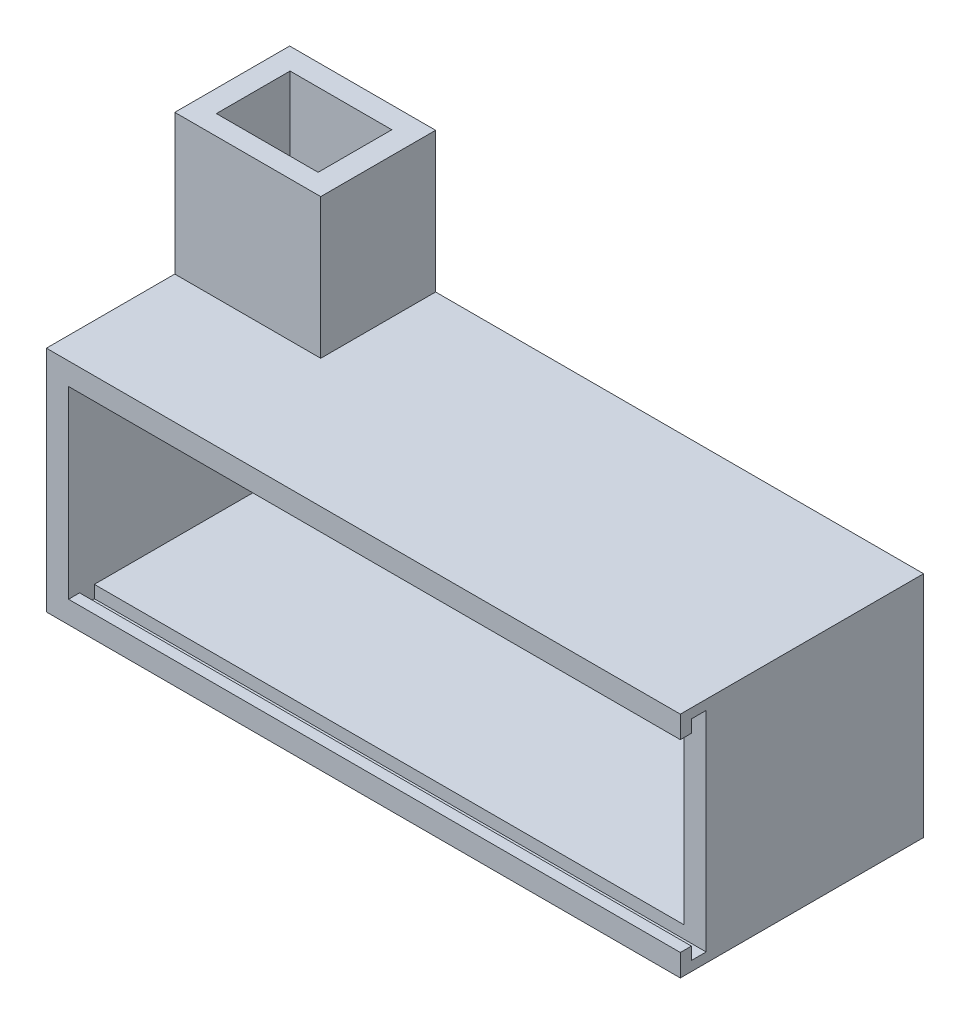
SolidWorks part; units mm, degrees
other "Marquage1"
sketch "Esquisse9" plane through (3, -3, 30) normal (0.8124, -0.2477, 0.5279) x (0.3571, 0.927, -0.1146)
ref_plane "Plan de face" through (0, 0, 0) normal (0, 0, 1) x (1, 0, 0)
ref_plane "Plan de dessus" through (0, 0, 0) normal (0, 1, 0) x (1, 0, 0)
ref_plane "Plan de droite" through (0, 0, 0) normal (1, 0, 0) x (0, 0, -1)
sketch "Esquisse1" plane through (0, 0, 0) normal (0, 0, 1) x (1, 0, 0)
  line L1 (0, 0) -> (-80, 0)
  line L2 (0, 0) -> (0, 25)
  line L3 (0, 25) -> (-80, 25)
  line L4 (-80, 0) -> (-80, 25)
  dimension "D1" = 80
  dimension "D2" = 25
extrude "Boss.-Extru.1" add sketch "Esquisse1" along normal blind 4
ref_plane "Plan1" through (0, 0, 0) normal (0, 0, -1) x (-1, 0, 0)
sketch "Esquisse3" plane through (0, 0, 0) normal (0, 0, -1) x (-1, 0, 0)
  line L0 (80, 25) -> (80, 0) construction
  line L1 (0, 0) -> (80, 0)
  line L2 (0, 0) -> (0, -3)
  line L3 (0, -3) -> (80, -3)
  line L4 (80, 0) -> (80, -3)
  dimension "D1" = 3
extrude "Boss.-Extru.2" add sketch "Esquisse3" against normal blind 28
ref_plane "Plan3" through (0, 12.5, 0) normal (0, 1, 0) x (1, 0, 0)
mirror "Symétrie1" about plane through (0, 12.5, 0) normal (0, 1, 0) of "Boss.-Extru.2"
sketch "Esquisse4" plane through (0, 0, 0) normal (1, 0, 0) x (0, 0, -1)
  line L1 (-28, 28) -> (0, 28)
  line L2 (-28, 28) -> (-28, -3)
  line L3 (-28, -3) -> (0, -3)
  line L4 (0, 28) -> (0, -3)
extrude "Boss.-Extru.3" add sketch "Esquisse4" along normal blind 3
sketch "Esquisse5" plane through (-80, 0, 0) normal (-1, 0, 0) x (0, 0, 1)
  line L1 (0, 28) -> (28, 28)
  line L2 (0, 28) -> (0, -3)
  line L3 (0, -3) -> (28, -3)
  line L4 (28, 28) -> (28, -3)
extrude "Boss.-Extru.4" add sketch "Esquisse5" along normal blind 3
sketch "Esquisse6" plane through (3, 0, 0) normal (1, 0, 0) x (0, 0, -1)
  line L0 (-33, 0) -> (-31.5, 0)
  line L1 (-28, -3) -> (-33, -3)
  line L2 (-28, -3) -> (-28, 0)
  line L3 (-28, 0) -> (-29.5, 0)
  line L4 (-33, -3) -> (-33, 0)
  line L5 (-31.5, 0) -> (-31.5, -1.6912)
  line L6 (-31.5, -1.6912) -> (-29.5, -1.6912)
  line L7 (-29.5, -1.6912) -> (-29.5, 0)
  line L8 (-29.5, 0) -> (-28, 0)
  line L9 (-31.5, 0) -> (-33, 0)
  line M7 (-28, 28) -> (-28, -3)
  dimension "D1" = 5
  dimension "D2" = 1.5
  dimension "D3" = 2
extrude "Boss.-Extru.5" add sketch "Esquisse6" against normal up to surface (86 mm away) contours L7 L6 L5 L0 L4 L1 L3 M7 up to face at (-83, 12.5, 14)
sketch "Esquisse7" plane through (-83, 0, 0) normal (-1, 0, 0) x (0, 0, 1)
  line L1 (28, 0) -> (33, 0)
  line L2 (28, 0) -> (28, -3)
  line L3 (28, -3) -> (33, -3)
  line L4 (33, 0) -> (33, -3)
extrude "Boss.-Extru.6" add sketch "Esquisse7" against normal up to surface (3 mm away) up to face at (-80, 12.5, 16)
mirror "Symétrie2" about plane through (0, 12.5, 0) normal (0, 1, 0) of "Boss.-Extru.6", "Boss.-Extru.5"
sketch "Esquisse8" plane through (0, 25, 0) normal (0, -1, 0) x (1, 0, 0)
  line L1 (-83, 33) -> (-80, 33)
  line L2 (-83, 33) -> (-83, 28)
  line L3 (-83, 28) -> (-80, 28)
  line L4 (-80, 33) -> (-80, 28)
extrude "Boss.-Extru.7" add sketch "Esquisse8" along normal up to surface (25 mm away) up to face at (-39.5, 0, 25.6667)
sketch "Esquisse10" plane through (0, 0, 28) normal (0, 0, 1) x (1, 0, 0)
  line L1 (0, 25) -> (3, 25)
  line L2 (0, 25) -> (0, 0)
  line L3 (0, 0) -> (3, 0)
  line L4 (3, 25) -> (3, 0)
extrude "Boss.-Extru.8" add sketch "Esquisse10" along normal up to surface (1.5 mm away) up to face at (-38.5, 25.8456, 29.5)
sketch "Esquisse11" plane through (0, 28, 0) normal (0, 1, 0) x (1, 0, 0)
  line L0 (3, 0) -> (-83, 0) construction
  line L9 (-83, -33) -> (-83, 0) construction
  line L10 (-80.0315, -2.9108) -> (-66.2311, -2.9108)
  line L11 (-83, -15.5865) -> (-63.1996, -15.5865)
  line L12 (-83, -15.5865) -> (-83, 0)
  line L13 (-83, 0) -> (-63.1996, 0)
  line L14 (-63.1996, -15.5865) -> (-63.1996, 0)
  line L15 (-80.0315, -2.9108) -> (-80.0315, -12.9108)
  line L16 (-80.0315, -12.9108) -> (-66.2311, -12.9108)
  line L17 (-66.2311, -2.9108) -> (-66.2311, -12.9108)
extrude "Boss.-Extru.9" add sketch "Esquisse11" along normal blind 19
sketch "Esquisse12" plane through (0, 28, 0) normal (0, 1, 0) x (1, 0, 0)
  line L1 (-80.0315, -2.9108) -> (-66.2311, -2.9108)
  line L2 (-80.0315, -2.9108) -> (-80.0315, -12.9108)
  line L3 (-80.0315, -12.9108) -> (-66.2311, -12.9108)
  line L4 (-66.2311, -2.9108) -> (-66.2311, -12.9108)
extrude "Enlèv. mat.-Extru.1" cut sketch "Esquisse12" against normal blind 3
